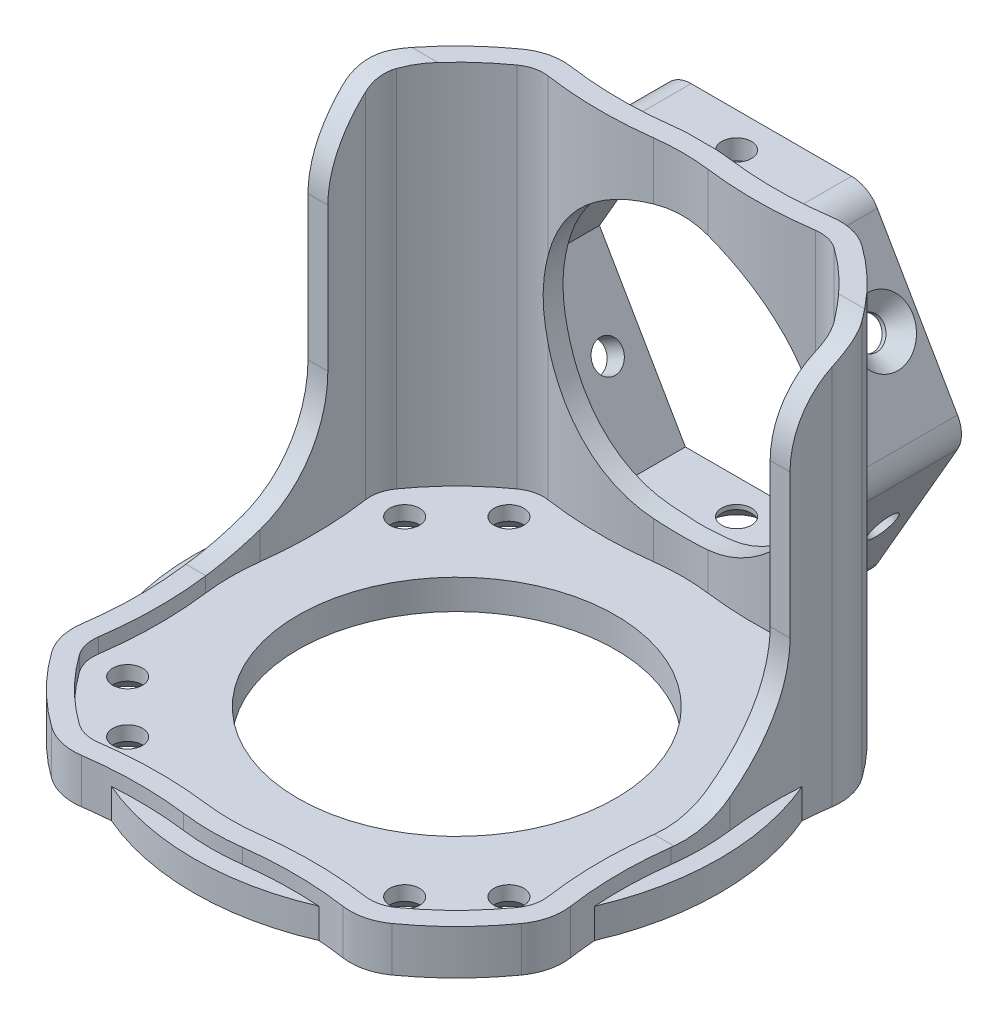
SolidWorks part; units mm, degrees
material "6061 合金"
ref_plane "前视基准面" through (0, 0, 0) normal (0, 0, 1) x (1, 0, 0)
ref_plane "上视基准面" through (0, 0, 0) normal (0, 1, 0) x (1, 0, 0)
ref_plane "右视基准面" through (0, 0, 0) normal (1, 0, 0) x (0, 0, -1)
sketch "草图1" plane through (0, 0, 0) normal (0, 1, 0) x (1, 0, 0)
  line L0 (0, 0) -> (0, 50.1956) construction
  line L1 (0, 0) -> (-38.5927, 0) construction
  line L2 (0, 0) -> (-19.2142, 13.9599) construction
  line L3 (-19.2142, 13.9599) -> (0, 0) construction
  line L4 (-13.9599, 19.2142) -> (0, 0) construction
  circle A0 centre (0, 0) radius 16
  circle A1 centre (0, 0) radius 26.5
  circle A2 centre (0, 0) radius 23.75 construction
  circle A3 centre (-19.2142, 13.9599) radius 1.5
  circle A4 centre (-13.9599, 19.2142) radius 1.5
  circle A5 centre (13.9599, 19.2142) radius 1.5
  circle A6 centre (19.2142, 13.9599) radius 1.5
  circle A7 centre (19.2142, -13.9599) radius 1.5
  circle A8 centre (13.9599, -19.2142) radius 1.5
  circle A9 centre (-19.2142, -13.9599) radius 1.5
  circle A10 centre (-13.9599, -19.2142) radius 1.5
  dimension "D1" = 32
  dimension "D2" = 47.5
  dimension "D3" = 3
  dimension "D6" = 53
  dimension "D4" = 36
  dimension "D5" = 36
extrude "凸台-拉伸1" add sketch "草图1" along normal blind 3
sketch "草图3" plane through (0, 3, 0) normal (0, 1, 0) x (1, 0, 0)
  line L0 (0, 0) -> (0, -34.5054) construction
  line L1 (0, 0) -> (28.4363, 0) construction
  line L2 (0, 0) -> (31.2107, -31.2107) construction
  arc A0 (-2.7377, -22.577) -> (2.7377, -22.577) centre (0, -1) ccw
  arc A1 (0, -21.75) -> (2.7345, -21.5774) centre (0, 0) ccw construction
  arc A2 (-2.9894, -24.5611) -> (2.9894, -24.5611) centre (0, -1) ccw
  arc A3 (2.7377, -22.577) -> (13.4637, -22.6658) centre (7.7725, -62.2589) cw
  arc A4 (13.5954, -21.6874) -> (2.7345, -21.5774) centre (7.7635, -61.26) ccw construction
  arc A5 (13.4637, -22.6658) -> (15.9902, -22.0493) centre (13.9599, -19.2142) ccw
  arc A6 (11.9599, -19.2142) -> (15.9599, -19.2142) centre (13.9599, -19.2142) ccw construction
  arc A7 (15.9902, -22.0493) -> (22.0493, -15.9902) centre (0.7071, -0.7071) ccw
  arc A8 (15.4294, -21.2367) -> (18.5616, -18.5616) centre (0, 0) ccw construction
  arc A9 (22.577, 2.7377) -> (22.577, -2.7377) centre (1, 0) cw
  arc A10 (22.577, -2.7377) -> (22.6658, -13.4637) centre (62.2589, -7.7725) ccw
  arc A11 (22.6658, -13.4637) -> (22.0493, -15.9902) centre (19.2142, -13.9599) cw
  arc A12 (-22.577, 2.7377) -> (-22.577, -2.7377) centre (-1, 0) ccw
  arc A13 (-22.577, -2.7377) -> (-22.6658, -13.4637) centre (-62.2589, -7.7725) cw
  arc A14 (-22.6658, -13.4637) -> (-22.0493, -15.9902) centre (-19.2142, -13.9599) ccw
  arc A15 (-15.9902, -22.0493) -> (-22.0493, -15.9902) centre (-0.7071, -0.7071) cw
  arc A16 (-13.4637, -22.6658) -> (-15.9902, -22.0493) centre (-13.9599, -19.2142) cw
  arc A17 (-2.7377, -22.577) -> (-13.4637, -22.6658) centre (-7.7725, -62.2589) ccw
  arc A18 (22.577, 2.7377) -> (22.6658, 13.4637) centre (62.2589, 7.7725) cw
  arc A19 (22.6658, 13.4637) -> (22.0493, 15.9902) centre (19.2142, 13.9599) ccw
  arc A20 (15.9902, 22.0493) -> (22.0493, 15.9902) centre (0.7071, 0.7071) cw
  arc A21 (13.4637, 22.6658) -> (15.9902, 22.0493) centre (13.9599, 19.2142) cw
  arc A22 (2.7377, 22.577) -> (13.4637, 22.6658) centre (7.7725, 62.2589) ccw
  arc A23 (-2.7377, 22.577) -> (2.7377, 22.577) centre (0, 1) cw
  arc A24 (-2.7377, 22.577) -> (-13.4637, 22.6658) centre (-7.7725, 62.2589) cw
  arc A25 (-13.4637, 22.6658) -> (-15.9902, 22.0493) centre (-13.9599, 19.2142) ccw
  arc A26 (-15.9902, 22.0493) -> (-22.0493, 15.9902) centre (-0.7071, 0.7071) ccw
  arc A27 (-22.6658, 13.4637) -> (-22.0493, 15.9902) centre (-19.2142, 13.9599) cw
  arc A28 (-22.577, 2.7377) -> (-22.6658, 13.4637) centre (-62.2589, 7.7725) ccw
  arc A29 (2.9894, -24.5611) -> (13.1792, -24.6455) centre (7.7725, -62.2589) cw
  arc A30 (13.1792, -24.6455) -> (17.1546, -23.6754) centre (13.9599, -19.2142) ccw
  arc A31 (17.1546, -23.6754) -> (20.6829, -20.6829) centre (0.7071, -0.7071) ccw
  arc A32 (23.6754, -17.1546) -> (20.6829, -20.6829) centre (0.7071, -0.7071) cw
  arc A33 (24.6455, -13.1792) -> (23.6754, -17.1546) centre (19.2142, -13.9599) cw
  arc A34 (24.5611, -2.9894) -> (24.6455, -13.1792) centre (62.2589, -7.7725) ccw
  arc A35 (24.5611, 2.9894) -> (24.5611, -2.9894) centre (1, 0) cw
  arc A36 (-2.9894, 24.5611) -> (2.9894, 24.5611) centre (0, 1) cw
  arc A37 (2.9894, 24.5611) -> (13.1792, 24.6455) centre (7.7725, 62.2589) ccw
  arc A38 (13.1792, 24.6455) -> (17.1546, 23.6754) centre (13.9599, 19.2142) cw
  arc A39 (17.1546, 23.6754) -> (20.6829, 20.6829) centre (0.7071, 0.7071) cw
  arc A40 (23.6754, 17.1546) -> (20.6829, 20.6829) centre (0.7071, 0.7071) ccw
  arc A41 (24.6455, 13.1792) -> (23.6754, 17.1546) centre (19.2142, 13.9599) ccw
  arc A42 (24.5611, 2.9894) -> (24.6455, 13.1792) centre (62.2589, 7.7725) cw
  arc A43 (-2.9894, -24.5611) -> (-13.1792, -24.6455) centre (-7.7725, -62.2589) ccw
  arc A44 (-13.1792, -24.6455) -> (-17.1546, -23.6754) centre (-13.9599, -19.2142) cw
  arc A45 (-17.1546, -23.6754) -> (-20.6829, -20.6829) centre (-0.7071, -0.7071) cw
  arc A46 (-23.6754, -17.1546) -> (-20.6829, -20.6829) centre (-0.7071, -0.7071) ccw
  arc A47 (-24.6455, -13.1792) -> (-23.6754, -17.1546) centre (-19.2142, -13.9599) ccw
  arc A48 (-24.5611, -2.9894) -> (-24.6455, -13.1792) centre (-62.2589, -7.7725) cw
  arc A49 (-24.5611, 2.9894) -> (-24.5611, -2.9894) centre (-1, 0) ccw
  arc A50 (-24.5611, 2.9894) -> (-24.6455, 13.1792) centre (-62.2589, 7.7725) ccw
  arc A51 (-24.6455, 13.1792) -> (-23.6754, 17.1546) centre (-19.2142, 13.9599) cw
  arc A52 (-23.6754, 17.1546) -> (-20.6829, 20.6829) centre (-0.7071, 0.7071) cw
  arc A53 (-17.1546, 23.6754) -> (-20.6829, 20.6829) centre (-0.7071, 0.7071) ccw
  arc A54 (-13.1792, 24.6455) -> (-17.1546, 23.6754) centre (-13.9599, 19.2142) ccw
  arc A55 (-2.9894, 24.5611) -> (-13.1792, 24.6455) centre (-7.7725, 62.2589) cw
  point P11 (14.7866, -22.6019)
  point P18 (0, -21.75)
  point P32 (18.5616, -18.5616)
  point P41 (22.6019, -14.7866)
  point P49 (-14.7866, -22.6019)
  point P79 (18.9801, -22.2515)
  point P82 (22.2515, -18.9801)
extrude "凸台-拉伸2" add sketch "草图3" along normal blind 37 and the other way blind 3
sketch "草图4" plane through (0, 0, 0) normal (1, 0, 0) x (0, 0, -1)
  line L0 (-27.9047, 4.5) -> (-2.7066, 4.5)
  line L1 (9.2934, 16.5) -> (9.2934, 31)
  line L2 (18.2934, 40) -> (24.7013, 40)
  line L3 (13.1792, 40) -> (2.9894, 40) construction
  line L4 (24.7013, 40) -> (24.7013, -2.0238)
  line L5 (24.7013, 0) -> (24.7013, 40) construction
  line L6 (-27.9047, 4.5) -> (-27.9047, 47.0536)
  line L7 (-27.9047, 47.0536) -> (30.5436, 47.0536)
  line L8 (30.5436, 47.0536) -> (30.5436, -2.0238)
  line L9 (30.5436, -2.0238) -> (24.7013, -2.0238)
  line L10 (-24.3532, 3) -> (-26.5, 3) construction
  arc A0 (-2.7066, 4.5) -> (9.2934, 16.5) centre (-2.7066, 16.5) ccw
  arc A1 (9.2934, 31) -> (18.2934, 40) centre (18.2934, 31) cw
  dimension "D1" = 12
  dimension "D2" = 9
  dimension "D3" = 1.5
extrude "切除-拉伸1" cut sketch "草图4" against normal through all and the other way through all
sketch "草图5" plane through (0, 0, -24.7013) normal (0, 0, -1) x (-1, 0, 0)
  line L0 (0, 8) -> (0, 40.3) construction
  line L1 (9.5966, 3) -> (1.5201, 3) construction
  circle A0 centre (0, 20.5) radius 14
  circle A1 centre (0, 20.5) radius 17.5 construction
  dimension "D1" = 28
  dimension "D2" = 35
extrude "切除-拉伸2" cut sketch "草图5" against normal blind 45
sketch "草图6" plane through (0, 40, 0) normal (0, 1, 0) x (1, 0, 0)
  line L0 (-13.1792, 24.6455) -> (-10.4923, 27.3324)
  line L1 (-10.4923, 27.3324) -> (-4.7068, 27.3324)
  line L2 (-4.7068, 27.3324) -> (-1.5201, 24.7013)
  line L3 (1.5201, 24.7013) -> (2.7707, 27.3324)
  line L4 (2.7707, 27.3324) -> (10.4432, 27.0412)
  line L5 (10.4432, 27.0412) -> (13.1792, 24.6455)
  arc A0 (1.5201, 24.7013) -> (2.9894, 24.5611) centre (0, 1) cw
  arc A1 (2.9894, 24.5611) -> (13.1792, 24.6455) centre (7.7725, 62.2589) ccw
  arc A2 (-1.5201, 24.7013) -> (-2.9894, 24.5611) centre (0, 1) ccw
  arc A3 (-2.9894, 24.5611) -> (-13.1792, 24.6455) centre (-7.7725, 62.2589) cw
extrude "切除-拉伸3" cut sketch "草图6" against normal blind 45
sketch "草图7" plane through (0, 0, -24.7013) normal (0, 0, -1) x (-1, 0, 0)
  line L1 (8.6603, 5.5) -> (17.3205, 20.5)
  line L2 (17.3205, 20.5) -> (8.6603, 35.5)
  line L3 (8.6603, 35.5) -> (-8.6603, 35.5)
  line L4 (-8.6603, 35.5) -> (-17.3205, 20.5)
  line L5 (-17.3205, 20.5) -> (-8.6603, 5.5)
  line L6 (-8.6603, 5.5) -> (8.6603, 5.5)
  line L7 (10.681, 5) -> (18.7639, 19)
  line L8 (18.7639, 22) -> (10.681, 36)
  line L9 (8.0829, 37.5) -> (-8.0829, 37.5)
  line L10 (-10.681, 36) -> (-18.7639, 22)
  line L11 (-18.7639, 19) -> (-10.681, 5)
  line L12 (-8.0829, 3.5) -> (8.0829, 3.5)
  circle A0 centre (0, 20.5) radius 15 construction
  arc A1 (13.1792, 25.2233) -> (2.9894, 34.1771) centre (0, 20.5) ccw construction
  circle A2 centre (0, 20.5) radius 17 construction
  arc A3 (10.681, 36) -> (8.0829, 37.5) centre (8.0829, 34.5) ccw
  arc A4 (18.7639, 19) -> (18.7639, 22) centre (16.1658, 20.5) ccw
  arc A5 (10.681, 5) -> (8.0829, 3.5) centre (8.0829, 6.5) cw
  arc A6 (-10.681, 5) -> (-8.0829, 3.5) centre (-8.0829, 6.5) ccw
  arc A7 (-18.7639, 22) -> (-18.7639, 19) centre (-16.1658, 20.5) ccw
  arc A8 (-8.0829, 37.5) -> (-10.681, 36) centre (-8.0829, 34.5) ccw
  dimension "D1" = 30
  dimension "D2" = 34
  dimension "D3" = 3
extrude "凸台-拉伸3" add sketch "草图7" along normal blind 7 and the other way blind 6
sketch "草图8" plane through (0, 40, 0) normal (0, 1, 0) x (1, 0, 0)
  line L0 (-22.0493, 15.9902) -> (22.0493, 15.9902)
  arc A0 (-22.0493, 15.9902) -> (-15.9902, 22.0493) centre (-0.7071, 0.7071) cw
  arc A1 (-15.9902, 22.0493) -> (-13.4637, 22.6658) centre (-13.9599, 19.2142) cw
  arc A2 (-13.4637, 22.6658) -> (-2.7377, 22.577) centre (-7.7725, 62.2589) ccw
  arc A3 (-2.7377, 22.577) -> (2.7377, 22.577) centre (0, 1) cw
  arc A4 (2.7377, 22.577) -> (13.4637, 22.6658) centre (7.7725, 62.2589) ccw
  arc A5 (13.4637, 22.6658) -> (15.9902, 22.0493) centre (13.9599, 19.2142) cw
  arc A6 (15.9902, 22.0493) -> (22.0493, 15.9902) centre (0.7071, 0.7071) cw
extrude "切除-拉伸4" cut sketch "草图8" against normal up to surface (37 mm away) up to face at (0, 3, 24.9493)
sketch "草图9" plane through (5.8457, -3.375, 0) normal (0.866, -0.5, 0) x (0, 0, -1)
  line L0 (31.7013, 17.7535) -> (28.2013, 17.7535) construction
  line L1 (31.7013, 25.8364) -> (31.7013, 9.6706) construction
  circle A0 centre (28.2013, 17.7535) radius 1.5
  dimension "D2" = 3
  dimension "D1" = 3.5
sketch "草图10" plane through (23.5992, 13.625, 0) normal (0.866, 0.5, 0) x (0, 0, -1)
  line L0 (31.7013, 17.7535) -> (28.2013, 17.7535) construction
  line L1 (31.7013, 25.8364) -> (31.7013, 9.6706) construction
  circle A0 centre (28.2013, 17.7535) radius 1.5
  dimension "D2" = 3
  dimension "D1" = 3.5
sketch "草图11" plane through (0, 37.5, 0) normal (0, 1, 0) x (1, 0, 0)
  line L0 (0, 31.7013) -> (0, 28.2013) construction
  line L1 (-8.0829, 31.7013) -> (8.0829, 31.7013) construction
  circle A0 centre (0, 28.2013) radius 1.5
  dimension "D2" = 3
  dimension "D1" = 3.5
extrude "切除-拉伸5" cut sketch "草图9" against normal through all
extrude "切除-拉伸6" cut sketch "草图10" against normal through all
extrude "切除-拉伸7" cut sketch "草图11" against normal through all
sketch "草图13" plane through (0, 0, 0) normal (0, -1, 0) x (1, 0, 0)
  line L0 (-15.3414, 23.7705) -> (-23.8773, 15.2346)
  line L1 (-23.8773, 15.2346) -> (-23.8773, 12.4211)
  line L2 (-23.8773, 12.4211) -> (-21.9936, 13.351)
  line L3 (-21.9936, 13.351) -> (-19.6093, 16.856)
  line L4 (-19.6093, 16.856) -> (-16.2117, 20.2536)
  line L5 (-16.2117, 20.2536) -> (-13.2745, 21.7036)
  line L6 (-13.2745, 21.7036) -> (-13.2745, 23.7705)
  line L7 (-13.2745, 23.7705) -> (-15.3414, 23.7705)
  line L8 (-23.5434, -13.1387) -> (-22.5897, -16.8106)
  line L9 (-22.5897, -16.8106) -> (-20.8015, -19.5287)
  line L10 (-20.8015, -19.5287) -> (-18.7152, -21.615)
  line L11 (-18.7152, -21.615) -> (-16.2117, -22.8667)
  line L12 (-16.2117, -22.8667) -> (-13.9895, -23.9778)
  line L13 (-13.9895, -23.9778) -> (-12.6233, -23.9778)
  line L14 (-12.6233, -23.9778) -> (-12.6233, -21.615)
  line L15 (-12.6233, -21.615) -> (-14.7431, -21.2454)
  line L16 (-14.7431, -21.2454) -> (-16.5444, -19.4441)
  line L17 (-16.5444, -19.4441) -> (-20.5318, -15.4567)
  line L18 (-20.5318, -15.4567) -> (-23.0666, -11.6038)
  line L19 (-23.0666, -11.6038) -> (-23.5434, -13.1387)
  line L20 (12.4234, -21.615) -> (13.0371, -23.9778)
  line L21 (13.0371, -23.9778) -> (15.8427, -23.2491)
  line L22 (15.8427, -23.2491) -> (19.6712, -20.7304)
  line L23 (19.6712, -20.7304) -> (22.1674, -17.4504)
  line L24 (22.1674, -17.4504) -> (23.4074, -14.9705)
  line L25 (23.4074, -14.9705) -> (23.4074, -13.5303)
  line L26 (23.4074, -13.5303) -> (21.8812, -13.0561)
  line L27 (21.8812, -13.0561) -> (20.6809, -15.4567)
  line L28 (20.6809, -15.4567) -> (18.9107, -17.2269)
  line L29 (18.9107, -17.2269) -> (16.7251, -19.0904)
  line L30 (16.7251, -19.0904) -> (15.1672, -20.6483)
  line L31 (15.1672, -20.6483) -> (13.6978, -21.615)
  line L32 (13.6978, -21.615) -> (12.4234, -21.615)
  line L33 (12.4234, 23.0972) -> (13.4832, 22.0374)
  line L34 (13.4832, 22.0374) -> (15.4588, 20.5339)
  line L35 (15.4588, 20.5339) -> (17.0571, 19.3175)
  line L36 (17.0571, 19.3175) -> (18.1598, 17.6413)
  line L37 (18.1598, 17.6413) -> (19.5861, 16.215)
  line L38 (19.5861, 16.215) -> (20.3097, 14.9845)
  line L39 (20.3097, 14.9845) -> (22.0095, 13.6908)
  line L40 (22.0095, 13.6908) -> (23.0963, 12.8638)
  line L41 (23.0963, 12.8638) -> (23.5689, 15.575)
  line L42 (23.5689, 15.575) -> (21.9203, 18.3788)
  line L43 (21.9203, 18.3788) -> (19.0885, 20.5339)
  line L44 (19.0885, 20.5339) -> (16.7251, 22.3326)
  line L45 (16.7251, 22.3326) -> (14.7606, 23.3148)
  line L46 (14.7606, 23.3148) -> (12.4234, 23.0972)
  circle A0 centre (19.2142, 13.9599) radius 1.5 construction
extrude "凸台-拉伸4" add sketch "草图13" against normal blind 3
chamfer "倒角1" distance 1.55 angle 45 8 edges at (19.2142, 0, -15.4599) (13.9599, 0, -20.7142) (-13.9599, 0, -17.7142) (-19.2142, 0, -12.4599) (-19.2142, 0, 12.4599) (-13.9599, 0, 17.7142) (19.2142, 0, 15.4599) (13.9599, 0, 20.7142)
chamfer "倒角2" distance 1.55 angle 45 3 edges at (-15.4724, 27.701, -28.2013) (13.9724, 30.299, -28.2013) (0, 3.5, -29.7013)
